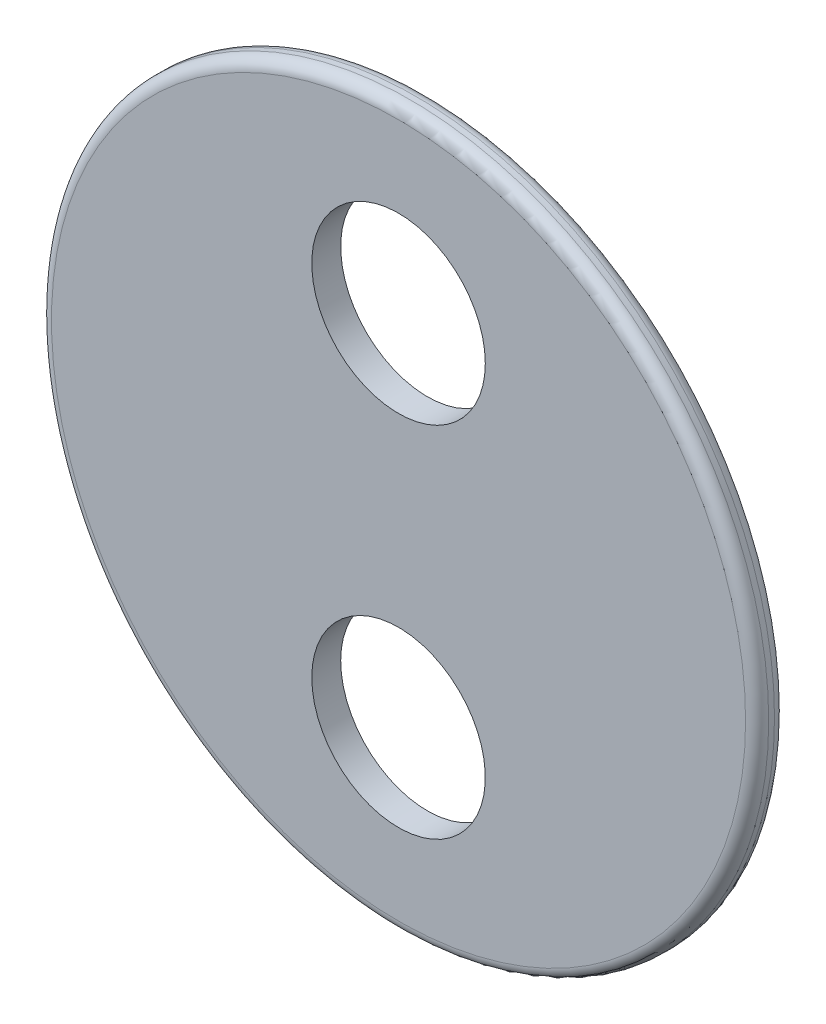
SolidWorks part; units mm, degrees
material "Copper"
ref_plane "Front Plane" through (0, 0, 0) normal (0, 0, 1) x (1, 0, 0)
ref_plane "Top Plane" through (0, 0, 0) normal (0, 1, 0) x (1, 0, 0)
ref_plane "Right Plane" through (0, 0, 0) normal (1, 0, 0) x (0, 0, -1)
sketch "Sketch2" plane through (0, 0, 0) normal (0, 0, 1) x (1, 0, 0)
  line L0 (0, 39.37) -> (0, 0) construction
  line L1 (55, 0) -> (-55, 0) construction
  circle A0 centre (0, 0) radius 39.37
  circle A1 centre (0, 19.685) radius 9.525
  circle A2 centre (0, -19.685) radius 9.525
  dimension "D1" = 78.74
  dimension "D2" = 19.05
extrude "Boss-Extrude2" add sketch "Sketch2" along normal blind 3.175
fillet "Fillet1" radius 1.27 2 edges at (39.37, 0, 0) (39.37, 0, 3.175)
